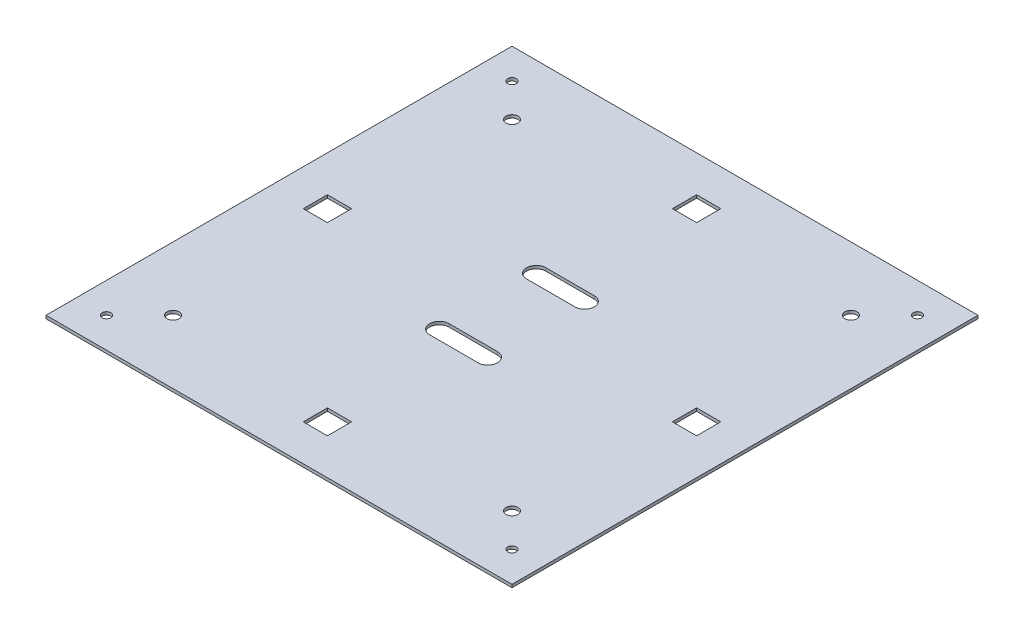
SolidWorks part; units mm, degrees
ref_plane "Front Plane" through (0, 0, 0) normal (0, 0, 1) x (1, 0, 0)
ref_plane "Top Plane" through (0, 0, 0) normal (0, 1, 0) x (1, 0, 0)
ref_plane "Right Plane" through (0, 0, 0) normal (1, 0, 0) x (0, 0, -1)
sketch "Sketch1" plane through (0, 0, 0) normal (0, 1, 0) x (1, 0, 0)
  line L1 (0, 0) -> (244.475, 0)
  line L2 (0, 0) -> (0, 244.475)
  line L3 (0, 244.475) -> (244.475, 244.475)
  line L4 (244.475, 0) -> (244.475, 244.475)
  dimension "D2" = 244.475
extrude "Main Body" add sketch "Sketch1" along normal blind 1.5875
sketch "Sketch2" plane through (0, 1.5875, 0) normal (0, 1, 0) x (1, 0, 0)
  line L0 (0, 0) -> (244.475, 0) construction
  line L1 (244.475, 0) -> (244.475, 244.475) construction
  line L2 (0, 0) -> (244.475, 244.475) construction
  line L4 (211.1375, 33.3375) -> (33.3375, 33.3375) construction
  line L5 (211.1375, 33.3375) -> (211.1375, 211.1375) construction
  line L6 (211.1375, 211.1375) -> (33.3375, 211.1375) construction
  line L7 (33.3375, 33.3375) -> (33.3375, 211.1375) construction
  circle A8 centre (211.1375, 33.3375) radius 3.175
  circle A12 centre (33.3375, 33.3375) radius 3.175
  circle A13 centre (33.3375, 211.1375) radius 3.175
  circle A14 centre (211.1375, 211.1375) radius 3.175
  circle A16 centre (228.6, 15.875) radius 2.286
  circle A17 centre (15.875, 15.875) radius 2.286
  circle A18 centre (15.875, 228.6) radius 2.286
  circle A19 centre (228.6, 228.6) radius 2.286
  point P10 (122.2375, 122.2375)
  point P19 (211.1375, 122.2375)
  point P20 (244.475, 122.2375)
  point P21 (122.2375, 33.3375)
  point P22 (122.2375, 0)
  dimension "D2" = 15.875
  dimension "D4" = 4.572
  dimension "D8" = 177.8
  dimension "D1" = 6.35
  dimension "D3" = 15.875
  dimension "D5" = 4
  dimension "D7" = 22.4506
  dimension "D6" = 177.8
extrude "Screw and String Holes" cut sketch "Sketch2" against normal through all
sketch "Sketch4" plane through (0, 1.5875, 0) normal (0, 1, 0) x (1, 0, 0)
  line L0 (0, 0) -> (244.475, 244.475) construction
  line L2 (115.8875, 31.75) -> (128.5875, 31.75)
  line L3 (115.8875, 31.75) -> (115.8875, 19.05)
  line L4 (115.8875, 19.05) -> (128.5875, 19.05)
  line L5 (128.5875, 31.75) -> (128.5875, 19.05)
  line L6 (19.05, 128.5875) -> (19.05, 115.8875)
  line L7 (31.75, 115.8875) -> (19.05, 115.8875)
  line L8 (31.75, 128.5875) -> (19.05, 128.5875)
  line L9 (31.75, 128.5875) -> (31.75, 115.8875)
  line L10 (128.5875, 225.425) -> (115.8875, 225.425)
  line L11 (115.8875, 212.725) -> (115.8875, 225.425)
  line L12 (128.5875, 212.725) -> (128.5875, 225.425)
  line L13 (128.5875, 212.725) -> (115.8875, 212.725)
  line L14 (225.425, 115.8875) -> (225.425, 128.5875)
  line L15 (212.725, 128.5875) -> (225.425, 128.5875)
  line L16 (212.725, 115.8875) -> (225.425, 115.8875)
  line L17 (212.725, 115.8875) -> (212.725, 128.5875)
  line L21 (0, 244.475) -> (0, 0) construction
  line L22 (0, 0) -> (244.475, 0) construction
  point P11 (122.2375, 122.2375)
  point P12 (122.2375, 122.2375)
  point P29 (19.05, 122.2375)
  point P30 (0, 122.2375)
  point P31 (122.2375, 19.05)
  point P32 (122.2375, 0)
  dimension "D1" = 12.7
  dimension "D2" = 12.7
  dimension "D3" = 19.05
  dimension "D5" = 19.05
  dimension "D4" = 4
extrude "LED Holes" cut sketch "Sketch4" against normal through all
sketch "Sketch5" plane through (0, 1.5875, 0) normal (0, 1, 0) x (1, 0, 0)
  line L0 (109.5375, 96.8375) -> (134.9375, 96.8375) construction
  line L1 (109.5375, 101.9175) -> (134.9375, 101.9175)
  line L2 (109.5375, 91.7575) -> (134.9375, 91.7575)
  line L3 (109.5375, 147.6375) -> (134.9375, 147.6375) construction
  line L4 (109.5375, 152.7175) -> (134.9375, 152.7175)
  line L5 (109.5375, 142.5575) -> (134.9375, 142.5575)
  line L6 (128.5875, 31.75) -> (115.8875, 31.75) construction
  line L7 (122.2375, 147.6375) -> (122.2375, 96.8375) construction
  line L9 (244.475, 0) -> (244.475, 244.475) construction
  arc A0 (109.5375, 101.9175) -> (109.5375, 91.7575) centre (109.5375, 96.8375) ccw
  arc A1 (134.9375, 91.7575) -> (134.9375, 101.9175) centre (134.9375, 96.8375) ccw
  arc A2 (109.5375, 152.7175) -> (109.5375, 142.5575) centre (109.5375, 147.6375) ccw
  arc A3 (134.9375, 142.5575) -> (134.9375, 152.7175) centre (134.9375, 147.6375) ccw
  point P2 (122.2375, 96.8375)
  point P9 (122.2375, 147.6375)
  point P17 (122.2375, 31.75)
  point P19 (122.2375, 122.2375)
  point P22 (244.475, 122.2375)
  dimension "D1" = 25.4
  dimension "D2" = 50.8
  dimension "D3" = 10.16
extrude "External Cable Slots" cut sketch "Sketch5" against normal through all
